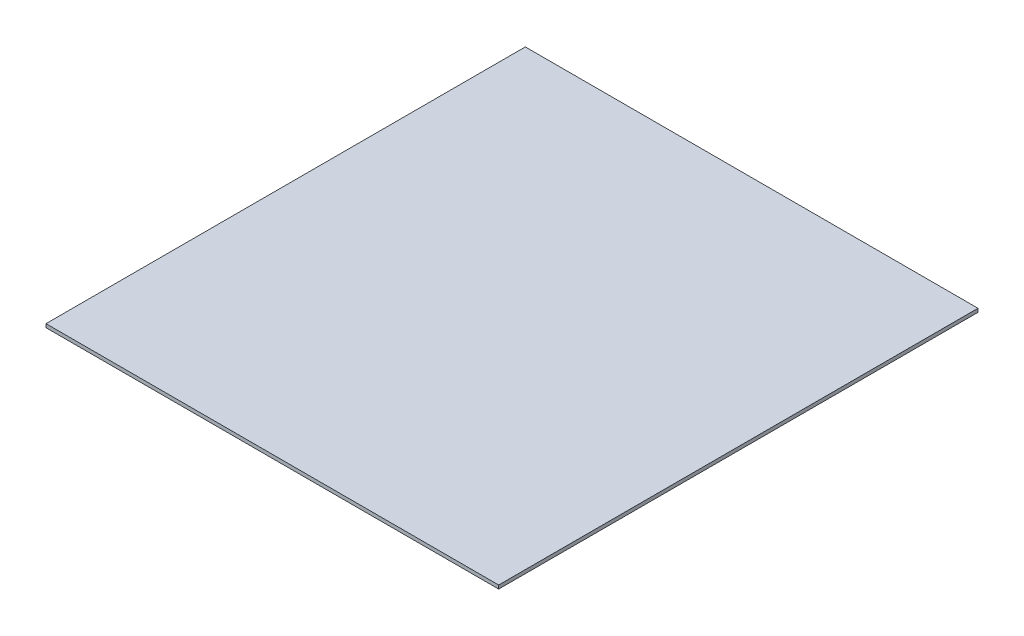
SolidWorks part; units mm, degrees
ref_plane "Front Plane" through (0, 0, 0) normal (0, 0, 1) x (1, 0, 0)
ref_plane "Top Plane" through (0, 0, 0) normal (0, 1, 0) x (1, 0, 0)
ref_plane "Right Plane" through (0, 0, 0) normal (1, 0, 0) x (0, 0, -1)
sketch "Sketch1" plane through (0, 0, 0) normal (0, 1, 0) x (1, 0, 0)
  line L1 (-255, 270) -> (255, 270)
  line L2 (-255, 270) -> (-255, -270)
  line L3 (-255, -270) -> (255, -270)
  line L4 (255, 270) -> (255, -270)
  line L5 (-255, 270) -> (255, -270) construction
  line L6 (-255, -270) -> (255, 270) construction
  point P0 (0, 0)
  dimension "D1" = 510
  dimension "D2" = 540
extrude "Boss-Extrude1" add sketch "Sketch1" along normal blind 4
